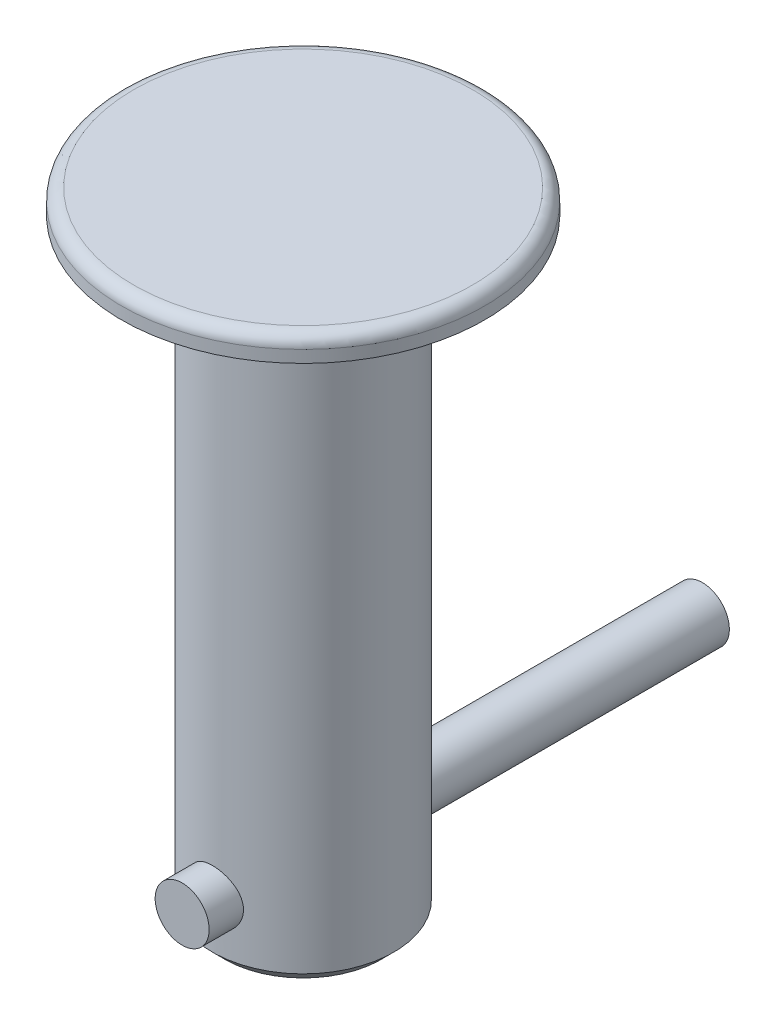
SolidWorks part; units mm, degrees
ref_plane "Ön Düzlem" through (0, 0, 0) normal (0, 0, 1) x (1, 0, 0)
ref_plane "Üst Düzlem" through (0, 0, 0) normal (0, 1, 0) x (1, 0, 0)
ref_plane "Sağ Düzlem" through (0, 0, 0) normal (1, 0, 0) x (0, 0, -1)
sketch "Çizim1" plane through (0, 0, 0) normal (0, 0, 1) x (1, 0, 0)
  line L1 (0, 0) -> (-15, 0)
  line L2 (0, 0) -> (0, 2)
  line L3 (0, 2) -> (-15, 2)
  line L4 (-15, 0) -> (-15, 2)
  line L5 (0, 0) -> (-7.5, 0)
  line L6 (0, 0) -> (0, -50)
  line L7 (0, -50) -> (-7.5, -50)
  line L8 (-7.5, 0) -> (-7.5, -50)
  dimension "D1" = 15
  dimension "D2" = 2
  dimension "D3" = 50
  dimension "D4" = 7.5
revolve "Döndür1" add sketch "Çizim1" angle 360 about L6
chamfer "Pah1" distance 1 angle 45 1 edges at (-7.5, -50, 0)
fillet "Radyus1" radius 1 1 edges at (-15, 2, 0)
sketch "Çizim2" plane through (0, 0, 0) normal (0, 0, 1) x (1, 0, 0)
  circle A0 centre (0, -45.0197) radius 2.2304
  point P2 (0, -45.0197)
extrude "Yükseklik-Ekstrüzyon1" add sketch "Çizim2" along normal blind 10 and the other way blind 33
